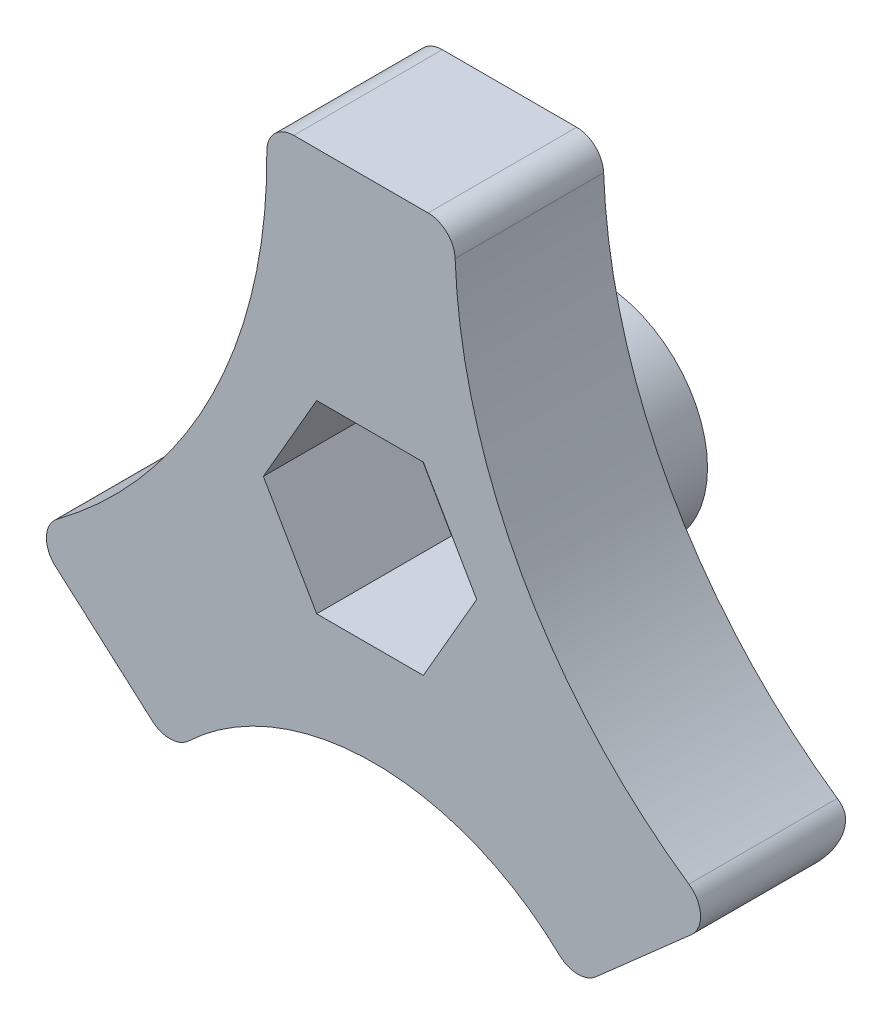
SolidWorks part; units mm, degrees
material "Rubber"
ref_plane "Front Plane" through (0, 0, 0) normal (0, 0, 1) x (1, 0, 0)
ref_plane "Top Plane" through (0, 0, 0) normal (0, 1, 0) x (1, 0, 0)
ref_plane "Right Plane" through (0, 0, 0) normal (1, 0, 0) x (0, 0, -1)
sketch "Sketch1" plane through (0, 0, 0) normal (0, 0, 1) x (1, 0, 0)
  line L1 (-3.8601, 18.642) -> (3.1399, 18.642)
  line L2 (7.6481, -3.3845) -> (12.8981, 1.2455)
  line L4 (-7.3519, -3.3845) -> (-12.6019, 1.2455)
  arc A0 (-7.3519, -3.3845) -> (7.6481, -3.3845) centre (0.1481, -9.9989) cw
  arc A1 (3.1399, 18.642) -> (12.8981, 1.2455) centre (23.1387, 18.4249) ccw
  arc A2 (-3.8601, 18.642) -> (-12.6019, 1.2455) centre (-23.0824, 17.4066) cw
  dimension "D3" = 10
  dimension "D1" = 20
  dimension "D2" = 7
  dimension "D4" = 15
extrude "Boss-Extrude1" add sketch "Sketch1" along normal blind 5.5
fillet "Fillet1" radius 1 7 edges at (10.2731, -1.0695, 0) (12.8981, 1.2455, 2.75) (-12.6019, 1.2455, 2.75) (-7.3519, -3.3845, 2.75) (-3.8601, 18.642, 2.75) (3.1399, 18.642, 2.75) (7.6481, -3.3845, 2.75)
sketch "Sketch2" plane through (0, 0, 0) normal (0, 0, -1) x (-1, 0, 0)
  line L0 (0, 0) -> (0, 18.642) construction
  line L1 (-2.1533, 18.642) -> (2.8218, 18.642) construction
  circle A0 centre (0, 7.142) radius 4
  dimension "D2" = 8
  dimension "D1" = 11.5
extrude "Boss-Extrude2" add sketch "Sketch2" along normal blind 3
sketch "Sketch3" plane through (0, 0, 5.5) normal (0, 0, 1) x (1, 0, 0)
  line L1 (2.1533, 18.642) -> (-2.8218, 18.642) construction
  line L3 (-3.95, 7.142) -> (-1.975, 3.7212)
  line L4 (-1.975, 3.7212) -> (1.975, 3.7212)
  line L5 (1.975, 3.7212) -> (3.95, 7.142)
  line L6 (3.95, 7.142) -> (1.975, 10.5628)
  line L7 (1.975, 10.5628) -> (-1.975, 10.5628)
  line L8 (-1.975, 10.5628) -> (-3.95, 7.142)
  circle A0 centre (0, 7.142) radius 3.4208 construction
  circle A2 centre (0, 7.142) radius 1.75
  arc A3 (7.0158, -2.7301) -> (-6.7195, -2.7301) centre (0.1481, -9.9989) ccw construction
  dimension "D3" = 13.7201
  dimension "D4" = 3.5
  dimension "D1" = 11.5
  dimension "D2" = 3.95
extrude "Cut-Extrude3" cut sketch "Sketch3" against normal blind 5
sketch "Sketch4" plane through (0, 0, -3) normal (0, 0, -1) x (-1, 0, 0)
  circle A0 centre (0, 7.142) radius 1.75
  dimension "D1" = 3.5
extrude "Cut-Extrude4" cut sketch "Sketch4" against normal through all
